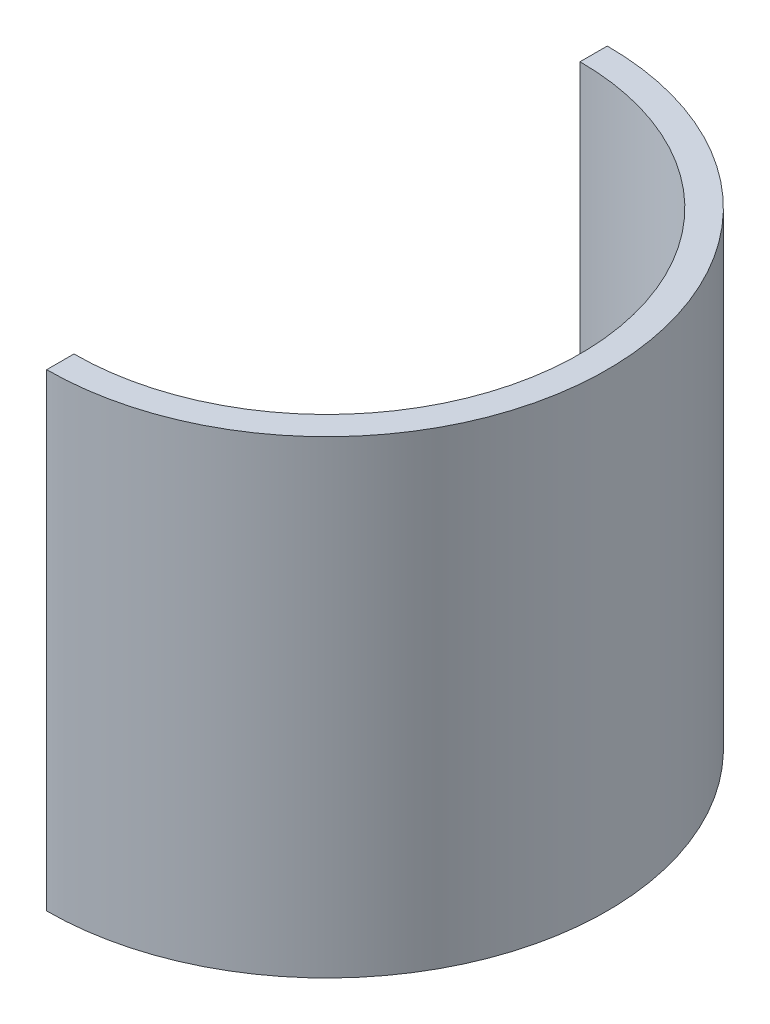
SolidWorks part; units mm, degrees
ref_plane "Front" through (0, 0, 0) normal (0, 0, 1) x (1, 0, 0)
ref_plane "Top" through (0, 0, 0) normal (0, 1, 0) x (1, 0, 0)
ref_plane "Right" through (0, 0, 0) normal (1, 0, 0) x (0, 0, -1)
sketch "草图1" plane through (0, 0, 0) normal (1, 0, 0) x (0, 0, -1)
  line L1 (9.1606, 43.4876) -> (14.1606, 43.4876)
  line L2 (9.1606, 43.4876) -> (9.1606, -42.5124)
  line L3 (9.1606, -42.5124) -> (14.1606, -42.5124)
  line L4 (14.1606, 43.4876) -> (14.1606, -42.5124)
  dimension "D1" = 5
  dimension "D2" = 86
sketch "草图2" plane through (0, 0, 0) normal (0, 1, 0) x (1, 0, 0)
  line L3 (0, 9.1606) -> (0, 38.6814) construction
  arc A0 (0, -83.6894) -> (0, 9.1606) centre (0, -37.2644) ccw
  point P1 (0, 0)
  point P4 (0, 0)
  point P6 (0, 0)
  point P7 (0, 0)
  point P8 (0, 0)
  point P9 (0, 0)
  point P10 (0, 0)
  point P11 (0, 0)
  dimension "D1" = 92.85
sweep "扫描1" add profiles "草图1" path "草图2"
